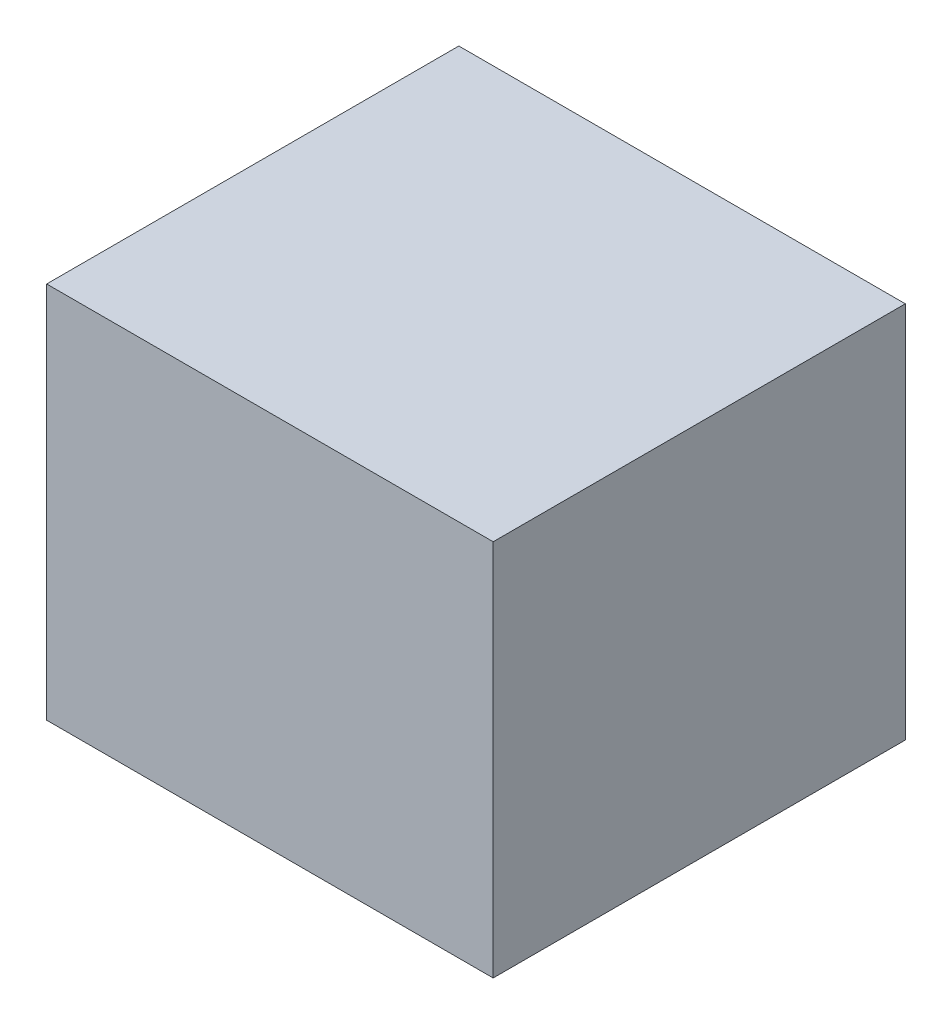
SolidWorks part; units mm, degrees
ref_plane "Front Plane" through (0, 0, 0) normal (0, 0, 1) x (1, 0, 0)
ref_plane "Top Plane" through (0, 0, 0) normal (0, 1, 0) x (1, 0, 0)
ref_plane "Right Plane" through (0, 0, 0) normal (1, 0, 0) x (0, 0, -1)
sketch "Sketch1" plane through (0, 0, 0) normal (0, 1, 0) x (1, 0, 0)
  line L0 (-825.5, 762) -> (825.5, -762) construction
  line L1 (-825.5, 762) -> (825.5, 762)
  line L2 (-825.5, 762) -> (-825.5, -762)
  line L3 (-825.5, -762) -> (825.5, -762)
  line L4 (825.5, 762) -> (825.5, -762)
  dimension "D1" = 1651
  dimension "D2" = 1524
extrude "Boss-Extrude1" add sketch "Sketch1" along normal blind 1397
